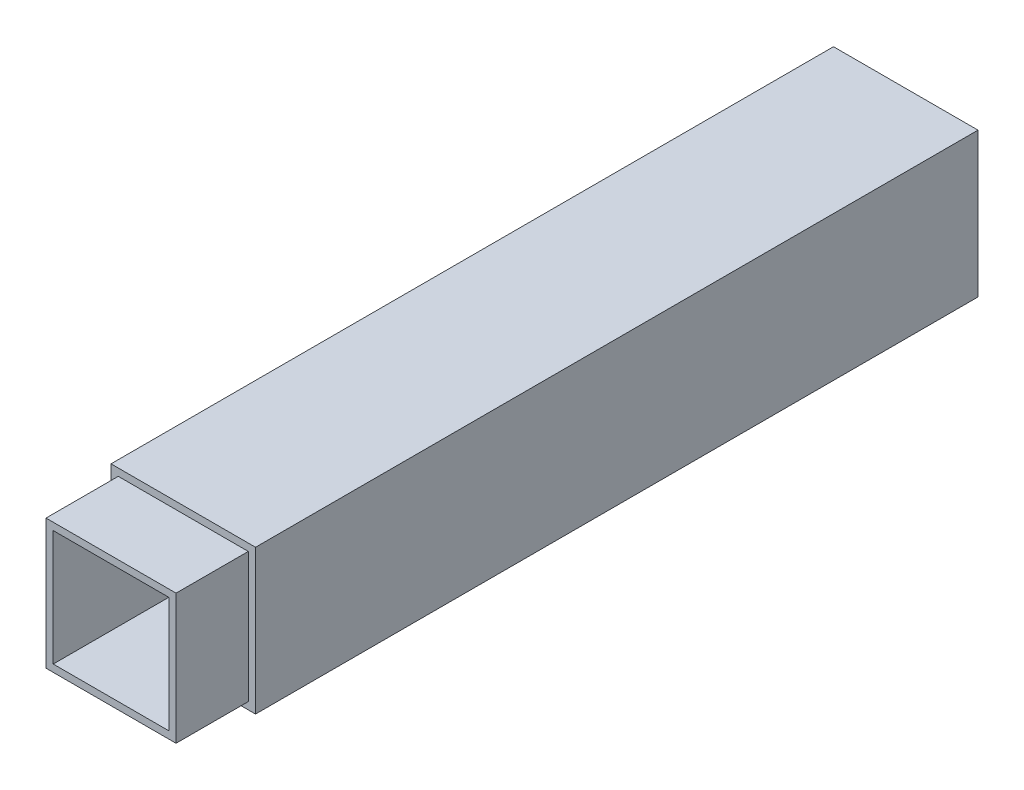
SolidWorks part; units mm, degrees
ref_plane "前基準面" through (0, 0, 0) normal (0, 0, 1) x (1, 0, 0)
ref_plane "上基準面" through (0, 0, 0) normal (0, 1, 0) x (1, 0, 0)
ref_plane "右基準面" through (0, 0, 0) normal (1, 0, 0) x (0, 0, -1)
sketch "草圖1" plane through (0, 0, 0) normal (0, 0, 1) x (1, 0, 0)
  line L0 (0, -55) -> (0, 55) construction
  line L1 (-10, 10) -> (10, 10)
  line L2 (-10, 10) -> (-10, -10)
  line L3 (-10, -10) -> (10, -10)
  line L4 (10, 10) -> (10, -10)
  line L5 (55, 0) -> (-55, 0) construction
  dimension "D1" = 20
  dimension "D2" = 20
  dimension "D3" = 10
  dimension "D4" = 10
extrude "填料-伸長1" add sketch "草圖1" along normal blind 100
sketch "草圖3" plane through (0, 0, 100) normal (0, 0, 1) x (1, 0, 0)
  line L0 (0, -11) -> (0, 11) construction
  line L1 (-9, 9) -> (9, 9)
  line L2 (-9, 9) -> (-9, -9)
  line L3 (-9, -9) -> (9, -9)
  line L4 (9, 9) -> (9, -9)
  line L5 (11, 0) -> (-11, 0) construction
  dimension "D1" = 18
  dimension "D2" = 18
  dimension "D3" = 9
  dimension "D4" = 9
extrude "填料-伸長2" add sketch "草圖3" along normal blind 10
sketch "草圖4" plane through (0, 0, 110) normal (0, 0, 1) x (1, 0, 0)
  line L1 (-8, 8) -> (8, 8)
  line L2 (-8, 8) -> (-8, -8)
  line L3 (-8, -8) -> (8, -8)
  line L4 (8, 8) -> (8, -8)
  line L5 (0, -11) -> (0, 11) construction
  line L6 (11, 0) -> (-11, 0) construction
  dimension "D1" = 16
  dimension "D2" = 16
  dimension "D3" = 8
  dimension "D4" = 8
extrude "除料-伸長1" cut sketch "草圖4" against normal blind 100
